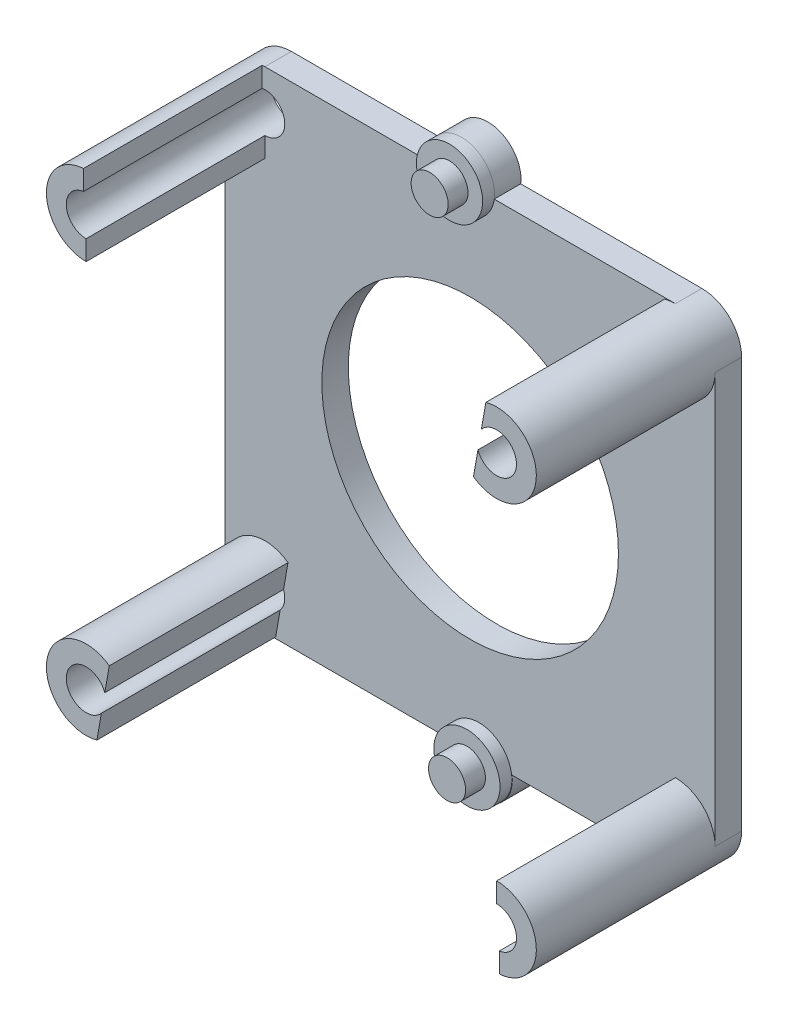
SolidWorks part; units mm, degrees
material "Titanium"
ref_plane "Front Plane" through (0, 0, 0) normal (0, 0, 1) x (1, 0, 0)
ref_plane "Top Plane" through (0, 0, 0) normal (0, 1, 0) x (1, 0, 0)
ref_plane "Right Plane" through (0, 0, 0) normal (1, 0, 0) x (0, 0, -1)
sketch "Sketch1" plane through (0, 0, 0) normal (0, 0, 1) x (1, 0, 0)
  line L0 (0, 0) -> (17.311, 13.1083) construction
  line L1 (0, 0) -> (-17.311, 13.1083) construction
  line L2 (15.5, 18.5) -> (-15.5, 18.5) construction
  line L3 (-18.5, 15.5) -> (-18.5, -15.5)
  line L4 (18.5, 15.5) -> (18.5, -15.5)
  line L5 (0, 0) -> (-0.657, 18.8134) construction
  line L6 (0, 0) -> (99.0761, 0) construction
  line L7 (15.5, -18.5) -> (-15.5, -18.5) construction
  line L8 (15.5, 18.5) -> (1.8193, 18.5)
  line L9 (-3.1333, 18.5) -> (-15.5, 18.5)
  line L10 (0, 0) -> (1.1952, -34.2261) construction
  line L11 (15.5, -18.5) -> (3.1677, -18.5)
  line L12 (-1.8538, -18.5) -> (-15.5, -18.5)
  circle A0 centre (0, 0) radius 11.2 construction
  circle A1 centre (15.5, 15.5) radius 1.5
  circle A2 centre (-15.5, 15.5) radius 1.5
  circle A3 centre (15.5, 15.5) radius 3 construction
  circle A4 centre (-15.5, 15.5) radius 3 construction
  circle A5 centre (0, 0) radius 11.2
  arc A6 (15.5, 18.5) -> (18.5, 15.5) centre (15.5, 15.5) cw
  arc A7 (18.5, -15.5) -> (15.5, -18.5) centre (15.5, -15.5) cw
  circle A8 centre (-0.657, 18.8134) radius 2.496 construction
  arc A9 (-3.1333, 18.5) -> (1.8193, 18.5) centre (-0.657, 18.8134) cw
  circle A10 centre (15.5, -15.5) radius 1.5
  circle A11 centre (-15.5, -15.5) radius 1.5
  circle A12 centre (15.5, -15.5) radius 3 construction
  circle A13 centre (-15.5, -15.5) radius 3 construction
  arc A14 (-15.5, -18.5) -> (-18.5, -15.5) centre (-15.5, -15.5) cw
  arc A15 (-18.5, 15.5) -> (-15.5, 18.5) centre (-15.5, 15.5) cw
  circle A16 centre (0.657, -18.8134) radius 2.5302 construction
  arc A17 (-1.8538, -18.5) -> (3.1677, -18.5) centre (0.657, -18.8134) ccw
  point P0 (0, 0)
  point P1 (15.5, 15.5)
  point P3 (-15.5, 15.5)
  point P20 (-0.657, 18.8134)
  point P25 (-15.5, -15.5)
  point P26 (15.5, -15.5)
  point P37 (0.657, -18.8134)
  dimension "D1" = 15.5
  dimension "D5" = 18.8249
  dimension "D6" = 15.5
  dimension "D2" = 15.5
  dimension "D3" = 15.5
  dimension "D4" = 15.5
  dimension "D7" = 15.5
  dimension "D8" = 15.5
  dimension "D9" = 15.5
  dimension "AXIS_DIST" = 18.8249
  dimension "ANGLE_AXIS" = 92
extrude "Extrude1" add sketch "Sketch1" along normal blind 2
sketch "Sketch2" plane through (0, 0, 2) normal (0, 0, 1) x (1, 0, 0)
  circle A0 centre (-0.657, 18.8134) radius 2.5
  circle A1 centre (0.657, -18.8134) radius 2.5
extrude "Extrude2" add sketch "Sketch2" along normal blind 0.9
sketch "Sketch3" plane through (0, 0, 2.9) normal (0, 0, 1) x (1, 0, 0)
  circle A0 centre (-0.657, 18.8134) radius 1.4
  circle A1 centre (0.657, -18.8134) radius 1.4
extrude "Extrude3" add sketch "Sketch3" along normal blind 1.5
sketch "Sketch4" plane through (0, 0, 2) normal (0, 0, 1) x (1, 0, 0)
  line L0 (3.1677, -18.5) -> (15.5, -18.5) construction
  line L1 (15.5, -14) -> (15.5, -12.5)
  line L2 (15.5, -17) -> (15.5, -18.5)
  line L3 (-14.8973, -12.5612) -> (-15.1987, -14.0306)
  line L4 (-15.8013, -16.9694) -> (-16.1027, -18.4388)
  line L5 (-15.5, 17) -> (-15.5, 18.5)
  line L6 (-15.5, 14) -> (-15.5, 12.5)
  line L7 (16.1027, 18.4388) -> (15.8013, 16.9694)
  line L8 (14.8973, 12.5612) -> (15.1987, 14.0306)
  line L9 (15.5, 15.5) -> (19.1993, 33.5387) construction
  line L10 (-0.657, 18.8134) -> (15.5, 15.5) construction
  line L11 (15.5, 15.5) -> (11.6647, -3.2016) construction
  line L12 (0.657, -18.8134) -> (-15.5, -15.5) construction
  line L13 (-15.5, -15.5) -> (-6.6358, 27.7235) construction
  line L14 (-15.5, -15.5) -> (-18.7803, -31.4956) construction
  circle A0 centre (-15.5, 15.5) radius 1.5 construction
  circle A2 centre (15.5, -15.5) radius 1.5 construction
  arc A4 (-15.5, 17) -> (-15.5, 14) centre (-15.5, 15.5) ccw
  arc A5 (-15.5, 18.5) -> (-15.5, 12.5) centre (-15.5, 15.5) ccw
  arc A6 (15.8013, 16.9694) -> (15.1987, 14.0306) centre (15.5, 15.5) cw
  circle A7 centre (15.5, 15.5) radius 1.5 construction
  arc A8 (-15.1987, -14.0306) -> (-15.8013, -16.9694) centre (-15.5, -15.5) ccw
  circle A9 centre (-15.5, -15.5) radius 1.5 construction
  arc A10 (15.5, -14) -> (15.5, -17) centre (15.5, -15.5) cw
  arc A11 (15.5, -18.5) -> (15.5, -12.5) centre (15.5, -15.5) ccw
  arc A12 (15.5, -18.5) -> (18.5, -15.5) centre (15.5, -15.5) ccw construction
  arc A13 (16.1027, 18.4388) -> (14.8973, 12.5612) centre (15.5, 15.5) cw
  arc A14 (18.5, 15.5) -> (15.5, 18.5) centre (15.5, 15.5) ccw construction
  arc A15 (-16.1027, -18.4388) -> (-14.8973, -12.5612) centre (-15.5, -15.5) cw
  arc A16 (-18.5, -15.5) -> (-15.5, -18.5) centre (-15.5, -15.5) ccw construction
  point P0 (-15.5, 14)
  point P1 (-15.5, 17)
  point P8 (15.5, -17)
  point P9 (15.5, -14)
  point P16 (-15.5, 18.5)
  point P50 (-0.657, 18.8134)
  point P51 (0.657, -18.8134)
extrude "Extrude4" add sketch "Sketch4" along normal blind 13.5
sketch "Sketch5" plane through (0, 0, 15.5) normal (0, 0, 1) x (1, 0, 0)
  line L0 (14.6847, 18.3871) -> (14.3482, 16.4609)
  line L1 (15.5, 15.5) -> (17.5127, 27.0192) construction
  line L2 (-15.5, -15.5) -> (-16.1691, -19.3296) construction
  line L3 (-15.5, -15.5) -> (-7.6977, -16.8632) construction
  line L4 (-14.0224, -15.7582) -> (-15.4682, -24.0329) construction
  line L5 (14.0906, 14.9866) -> (13.7541, 13.0604)
  line L6 (15.5, 15.5) -> (14.0509, 7.2061) construction
  line L7 (15.5, 15.5) -> (8.4826, 16.7261) construction
  line L8 (14.0224, 15.7582) -> (16.5611, 30.2881) construction
  line L9 (16.6695, 29.7463) -> (12.0372, 3.2345) construction
  line L10 (-15.5928, -23.5844) -> (-13.0569, -9.0702) construction
  line L11 (-13.7541, -13.0604) -> (-14.0906, -14.9866)
  line L12 (-14.3482, -16.4609) -> (-14.6847, -18.3871)
  circle A0 centre (15.5, 15.5) radius 1.5 construction
  circle A1 centre (-15.5, -15.5) radius 1.5 construction
  circle A2 centre (15.5, 15.5) radius 3 construction
  circle A3 centre (-15.5, -15.5) radius 3 construction
  arc A4 (14.3482, 16.4609) -> (14.0906, 14.9866) centre (15.5, 15.5) cw
  arc A5 (14.6847, 18.3871) -> (13.7541, 13.0604) centre (15.5, 15.5) cw
  arc A6 (-14.3482, -16.4609) -> (-14.0906, -14.9866) centre (-15.5, -15.5) cw
  arc A7 (-14.6847, -18.3871) -> (-13.7541, -13.0604) centre (-15.5, -15.5) cw
  dimension "D1" = 0.2
  dimension "D2" = 0.2
extrude "Extrude5" add sketch "Sketch5" against normal blind 13.5
sketch "Sketch6" plane through (0, 0, 15.5) normal (0, 0, 1) x (1, 0, 0)
  line L0 (-15.5, 13.25) -> (-15.5, 23.3935) construction
  line L1 (-15.5, 12.5) -> (-15.5, 14) construction
  line L2 (-15.7, 23.8125) -> (-15.7, 7.9375) construction
  line L3 (-15.5, 19.6178) -> (-15.5, 15.8619)
  line L4 (-15.5, 15.8619) -> (-15.7, 15.875)
  line L5 (-15.7, 15.875) -> (-15.7, 19.6178)
  line L6 (-15.7, 19.6178) -> (-15.5, 19.6178)
  line L7 (15.5, -13.25) -> (15.5, -24.1122) construction
  line L8 (15.5, -12.5) -> (15.5, -14) construction
  line L9 (15.7, -26.9875) -> (15.7, 0) construction
  line L10 (15.5, -20.264) -> (15.5, -15.9249)
  line L11 (15.5, -15.9249) -> (15.7, -15.9249)
  line L12 (15.7, -15.9249) -> (15.7, -20.264)
  line L13 (15.7, -20.264) -> (15.5, -20.264)
  point P6 (-15.5, 19.6178)
  point P17 (15.5, -20.264)
  dimension "D1" = 0.2
  dimension "D2" = 0.2
extrude "Extrude6" cut sketch "Sketch6" against normal blind 13.5
equation "\"D5@Sketch1\" = \"AXIS_DIST\""
